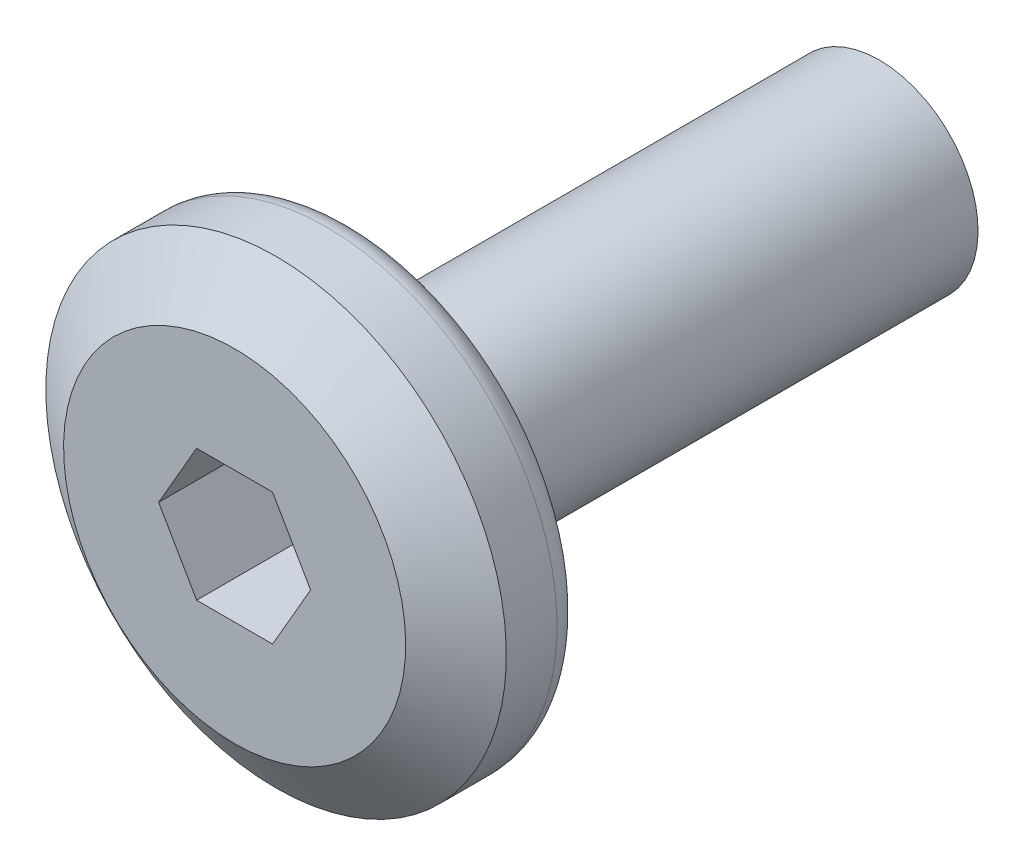
SolidWorks part; units mm, degrees
material "AISI 304"
ref_plane "前视基准面" through (0, 0, 0) normal (0, 0, 1) x (1, 0, 0)
ref_plane "上视基准面" through (0, 0, 0) normal (0, 1, 0) x (1, 0, 0)
ref_plane "右视基准面" through (0, 0, 0) normal (1, 0, 0) x (0, 0, -1)
sketch "草图2" plane through (0, 0, 0) normal (1, 0, 0) x (0, 0, -1)
  line L0 (0, 0) -> (0, 3.5)
  line L1 (0, 3.5) -> (1.8, 3.5)
  line L2 (1.8, 3.5) -> (1.8, 1.5)
  line L3 (1.8, 1.5) -> (9.8, 1.5)
  line L4 (9.8, 1.5) -> (9.8, 0)
  line L5 (9.8, 0) -> (0, 0) construction
  line L6 (0, 0) -> (9.8, 0)
  dimension "D1" = 7
  dimension "D2" = 1.8
  dimension "D3" = 8
  dimension "D4" = 3
revolve "旋转1" add sketch "草图2" angle 360 about L5
cosmetic thread "装饰螺纹线1" parameters "D2"=2
chamfer "倒角1" distance 0.9 angle 35 1 edges at (0, 3.5, 0)
sketch "草图3" plane through (0, 0, 0) normal (0, 0, 1) x (1, 0, 0)
  line L1 (0.5774, 1) -> (-0.5774, 1)
  line L2 (-0.5774, 1) -> (-1.1547, 0)
  line L3 (-1.1547, 0) -> (-0.5774, -1)
  line L4 (-0.5774, -1) -> (0.5774, -1)
  line L5 (0.5774, -1) -> (1.1547, 0)
  line L6 (1.1547, 0) -> (0.5774, 1)
  circle A0 centre (0, 0) radius 1 construction
  dimension "D1" = 2
extrude "切除-拉伸1" cut sketch "草图3" against normal blind 1.5
fillet "圆角1" radius 0.4 1 edges at (0, 3.5, -1.8)
